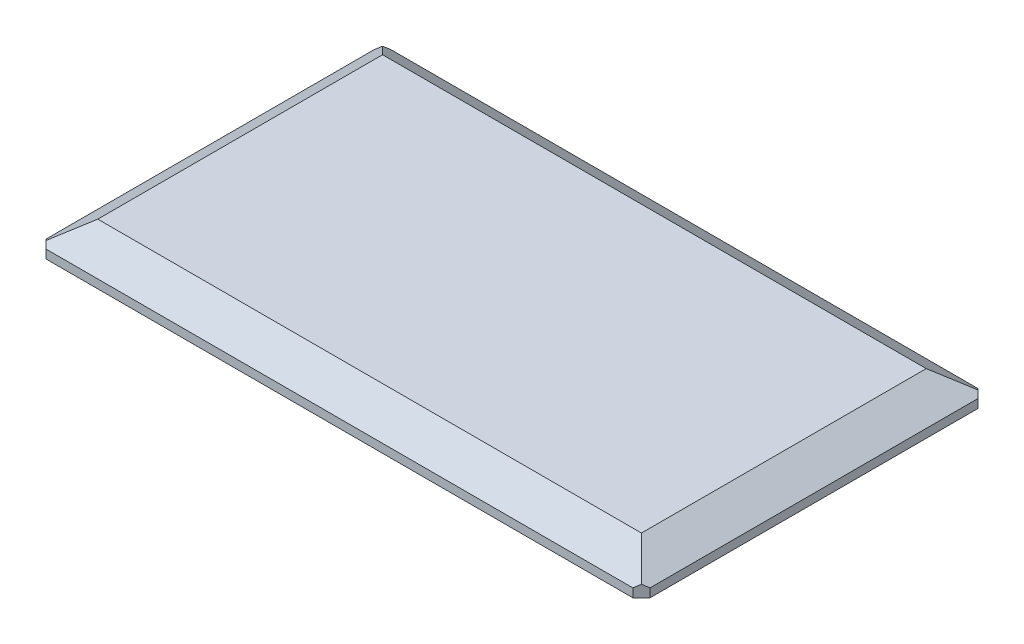
SolidWorks part; units mm, degrees
ref_plane "Front Plane" through (0, 0, 0) normal (0, 0, 1) x (1, 0, 0)
ref_plane "Top Plane" through (0, 0, 0) normal (0, 1, 0) x (1, 0, 0)
ref_plane "Right Plane" through (0, 0, 0) normal (1, 0, 0) x (0, 0, -1)
sketch "Sketch1" plane through (0, 0, 0) normal (0, 1, 0) x (1, 0, 0)
  line L1 (-70, -40) -> (70, -40)
  line L2 (-70, -40) -> (-70, 40)
  line L3 (-70, 40) -> (70, 40)
  line L4 (70, -40) -> (70, 40)
  line L5 (-70, -40) -> (70, 40) construction
  line L6 (-70, 40) -> (70, -40) construction
  point P0 (0, 0)
  dimension "D1" = 140
  dimension "D2" = 80
extrude "Boss-Extrude1" add sketch "Sketch1" along normal blind 2
sketch "Sketch2" plane through (0, 2, 0) normal (0, 1, 0) x (1, 0, 0)
  line L4 (70, -40) -> (70, 40)
  line L5 (70, 40) -> (-70, 40)
  line L6 (-70, 40) -> (-70, -40)
  line L7 (-70, -40) -> (70, -40)
  line L8 (70, -40) -> (70, 40)
  line L9 (70, 40) -> (-70, 40)
  line L10 (-70, 40) -> (-70, -40)
  line L11 (-70, -40) -> (70, -40)
  dimension "D1" = 0
ref_plane "Plane1" through (0, 7, 0) normal (0, 1, 0) x (1, 0, 0)
sketch "Sketch3" plane through (0, 7, 0) normal (0, 1, 0) x (1, 0, 0)
  line L0 (-70, 40) -> (-70, -40) construction
  line L1 (-63, -33) -> (63, -33)
  line L2 (-63, -33) -> (-63, 33)
  line L3 (-63, 33) -> (63, 33)
  line L4 (63, -33) -> (63, 33)
  line L5 (-63, -33) -> (63, 33) construction
  line L6 (-63, 33) -> (63, -33) construction
  line L7 (70, 40) -> (-70, 40) construction
  point P0 (0, 0)
  dimension "D1" = 7
  dimension "D2" = 7
loft "Loft1" add profiles "Sketch3", "Sketch2"
chamfer "Chamfer2" distance 2 angle 45 4 edges at (70, 1, 40) (70, 1, -40) (-70, 1, -40) (-70, 1, 40)
sketch "Sketch4" plane through (0, 0, 0) normal (0, -1, 0) x (1, 0, 0)
  line L0 (-70, -38) -> (-70, 38) construction
  line L1 (-62.9, 15) -> (-54.9, 15)
  line L2 (-62.9, 15) -> (-62.9, 25)
  line L3 (-62.9, 25) -> (-54.9, 25)
  line L4 (-54.9, 15) -> (-54.9, 25)
  line L5 (-62.9, 15) -> (-54.9, 25) construction
  line L6 (-62.9, 25) -> (-54.9, 15) construction
  line L7 (-70, 0) -> (70, 0) construction
  line L8 (70, 38) -> (70, -38) construction
  line L9 (0, 40) -> (0, -40) construction
  line L10 (-68, 40) -> (68, 40) construction
  line L11 (68, -40) -> (-68, -40) construction
  line L12 (-62.9, -25) -> (-54.9, -15) construction
  line L13 (-62.9, -15) -> (-54.9, -25) construction
  line L14 (-54.9, -15) -> (-54.9, -25)
  line L15 (-62.9, -25) -> (-54.9, -25)
  line L16 (-62.9, -15) -> (-62.9, -25)
  line L17 (-62.9, -15) -> (-54.9, -15)
  line L18 (62.9, -15) -> (54.9, -25) construction
  line L19 (62.9, -25) -> (54.9, -15) construction
  line L20 (62.9, 25) -> (54.9, 15) construction
  line L21 (62.9, 15) -> (54.9, 25) construction
  line L22 (62.9, -15) -> (54.9, -15)
  line L23 (62.9, -15) -> (62.9, -25)
  line L24 (62.9, -25) -> (54.9, -25)
  line L25 (54.9, -15) -> (54.9, -25)
  line L26 (54.9, 15) -> (54.9, 25)
  line L27 (62.9, 25) -> (54.9, 25)
  line L28 (62.9, 15) -> (62.9, 25)
  line L29 (62.9, 15) -> (54.9, 15)
  point P0 (-58.9, 20)
  point P21 (-58.9, -20)
  point P30 (58.9, -20)
  point P31 (58.9, 20)
  dimension "D1" = 10
  dimension "D2" = 7.1
  dimension "D3" = 8
  dimension "D4" = 40
extrude "Boss-Extrude2" add sketch "Sketch4" along normal blind 7
sketch "Sketch5" plane through (-62.9, 0, 0) normal (-1, 0, 0) x (0, 0, 1)
  line L0 (-15, 0) -> (-25, -7) construction
  line L1 (0, 0) -> (0, 50000) construction
  circle A0 centre (-20, -3.5) radius 2.05
  circle A1 centre (20, -3.5) radius 2.05
  dimension "D1" = 4.1
extrude "Cut-Extrude1" cut sketch "Sketch5" against normal through all
sketch "Sketch6" plane through (0, 0, 0) normal (0, -1, 0) x (1, 0, 0)
  line L0 (54.9, 25) -> (54.9, 15) construction
  line L1 (-53.9, -32) -> (53.9, -32)
  line L2 (-53.9, -32) -> (-53.9, 32)
  line L3 (-53.9, 32) -> (53.9, 32)
  line L4 (53.9, -32) -> (53.9, 32)
  line L5 (-53.9, -32) -> (53.9, 32) construction
  line L6 (-53.9, 32) -> (53.9, -32) construction
  line L8 (-63, 33) -> (63, 33) construction
  point P0 (0, 0)
  point P8 (50.8662, 32)
  dimension "D1" = 1
  dimension "D2" = 1
extrude "Cut-Extrude2" cut sketch "Sketch6" against normal offset from surface (5 mm away) 2 up to face at (0, 7, 0)
